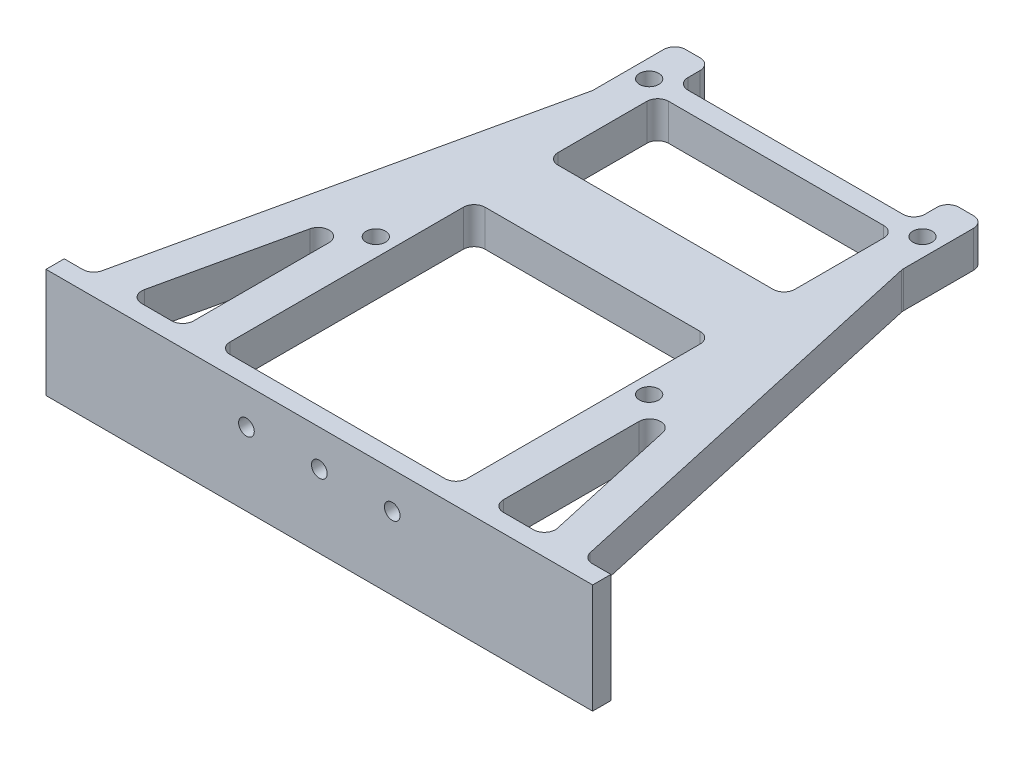
SolidWorks part; units mm, degrees
ref_plane "前视基准面" through (0, 0, 0) normal (0, 0, 1) x (1, 0, 0)
ref_plane "上视基准面" through (0, 0, 0) normal (0, 1, 0) x (1, 0, 0)
ref_plane "右视基准面" through (0, 0, 0) normal (1, 0, 0) x (0, 0, -1)
other "Configuration Table"
sketch "Sketch1" plane through (0, 0, 0) normal (0, 0, 1) x (1, 0, 0)
  line L1 (0, 0) -> (150, 0)
  line L2 (0, 0) -> (0, 30)
  line L3 (0, 30) -> (150, 30)
  line L4 (150, 0) -> (150, 30)
  dimension "D1" = 30
  dimension "D2" = 150
extrude "Boss-Extrude1" add sketch "Sketch1" along normal blind 5
sketch "Sketch2" plane through (0, 0, 5) normal (0, 0, 1) x (1, 0, 0)
  line L0 (150, 30) -> (0, 30) construction
  line L1 (0, 30) -> (0, 0) construction
  line L2 (75, 30) -> (75, 0) construction
  line L3 (0, 0) -> (150, 0) construction
  circle A0 centre (75, 20) radius 2.15
  circle A1 centre (55, 20) radius 2.15
  circle A2 centre (95, 20) radius 2.15
  point P12 (0, 0)
  point P15 (55, 10)
  point P16 (0, 0)
  dimension "D2" = 4.3
  dimension "D3" = 75
  dimension "D4" = 4.3
  dimension "D5" = 40
  dimension "D1" = 10
extrude "Cut-Extrude1" cut sketch "Sketch2" against normal through all
sketch "Sketch3" plane through (0, 30, 0) normal (0, 1, 0) x (1, 0, 0)
  line L0 (75, 0) -> (75, -5) construction
  line L1 (150, 0) -> (0, 0) construction
  line L2 (150, -5) -> (0, -5) construction
  line L3 (107.5, 0) -> (107.5, 135)
  line L8 (32.5, 0) -> (42.5, 0)
  line L9 (32.5, 0) -> (32.5, 135)
  line L10 (32.5, 135) -> (42.5, 135)
  line L11 (42.5, 0) -> (42.5, 135)
  line L12 (117.5, 135) -> (107.5, 135)
  line L13 (117.5, 0) -> (117.5, 135)
  line L14 (117.5, 0) -> (107.5, 0)
  dimension "D1" = 75
  dimension "D2" = 10
  dimension "D3" = 135
extrude "Boss-Extrude2" add sketch "Sketch3" against normal blind 10 contours L9 L8 L11 L10 | L3 L12 L13 L14
sketch "Sketch4" plane through (0, 30, 0) normal (0, 1, 0) x (1, 0, 0)
  line L0 (32.5, 112.5) -> (7.5, 0)
  line L1 (32.5, 0) -> (32.5, 135) construction
  line L2 (32.5, 0) -> (0, 0) construction
  line L3 (7.5, 0) -> (17.5, 0)
  line L4 (7.5, 0) -> (17.5, 0)
  line L5 (17.5, 0) -> (32.5, 67.5)
  line L6 (32.5, 67.5) -> (32.5, 112.5)
  line L7 (75, 0) -> (75, -5) construction
  line L8 (107.5, 0) -> (42.5, 0) construction
  line L9 (150, -5) -> (0, -5) construction
  line L10 (117.5, 67.5) -> (117.5, 112.5)
  line L11 (132.5, 0) -> (117.5, 67.5)
  line L12 (142.5, 0) -> (132.5, 0)
  line L13 (142.5, 0) -> (132.5, 0)
  line L14 (117.5, 112.5) -> (142.5, 0)
  line M7 (150, 0) -> (117.5, 0)
  line M8 (117.5, 0) -> (117.5, 135)
  line M14 (32.5, 135) -> (32.5, 0)
  line M15 (32.5, 0) -> (0, 0)
  dimension "D1" = 10
  dimension "D2" = 15
extrude "Boss-Extrude3" add sketch "Sketch4" against normal up to surface (10 mm away) contours L5 L0 M15 M14 | L14 L11 M8 M7 up to face at (112.5, 20, -67.5)
sketch "Sketch5" plane through (0, 30, 0) normal (0, 1, 0) x (1, 0, 0)
  line L0 (107.5, 0) -> (42.5, 0) construction
  line L1 (107.5, 0) -> (42.5, 0) construction
  line L4 (32.5, 0) -> (32.5, 67.5) construction
  circle A0 centre (37.5, 48) radius 2.65
  circle A1 centre (112.5, 48) radius 2.65
  circle A2 centre (112.5, 123) radius 2.65
  circle A3 centre (37.5, 123) radius 2.65
  point P4 (123.0822, 122.2497)
  point P7 (0, 0)
  dimension "D1" = 5.3
  dimension "D6" = 75
  dimension "D7" = 75
  dimension "D2" = 48
  dimension "D3" = 5
  dimension "D4" = 2
  dimension "D5" = 2
sketch "Sketch6" plane through (107.5, 0, 0) normal (-1, 0, 0) x (0, 0, 1)
  line L0 (-112.5, 30) -> (0, 30) construction
  line L1 (-90, 30) -> (-70, 30)
  line L2 (-90, 30) -> (-90, 20)
  line L3 (-90, 20) -> (-70, 20)
  line L4 (-70, 30) -> (-70, 20)
  line L5 (-112.5, 20) -> (0, 20) construction
  dimension "D1" = 20
  dimension "D2" = 45
extrude "Boss-Extrude4" add sketch "Sketch6" along normal up to surface (65 mm away) up to face at (42.5, 25, -67.5)
extrude "Cut-Extrude3" cut sketch "Sketch5" against normal blind 10
sketch "Sketch7" plane through (107.5, 0, 0) normal (-1, 0, 0) x (0, 0, 1)
  line L0 (-125.65, 20) -> (-120.35, 20) construction
  line L1 (-125.65, 20) -> (-120.35, 20)
  line L2 (-125.65, 20) -> (-125.65, 30)
  line L3 (-125.65, 30) -> (-120.35, 30)
  line L4 (-120.35, 30) -> (-120.35, 20)
extrude "Boss-Extrude5" add sketch "Sketch7" along normal up to next
fillet "Fillet1" radius 3 20 edges at (32.5, 25, -135) (32.5, 25, -112.5) (7.5, 25, 0) (17.5, 25, 0) (32.5, 25, -67.5) (32.5, 25, 0) (42.5, 25, 0) (42.5, 25, -70) (107.5, 25, -70) (107.5, 25, 0) (117.5, 25, 0) (117.5, 25, -67.5) (132.5, 25, 0) (142.5, 25, 0) (117.5, 25, -112.5) (117.5, 25, -135) (107.5, 25, -135) (42.5, 25, -135) (42.5, 25, -125.65) (107.5, 25, -125.65)
fillet "Fillet2" radius 3 4 edges at (42.5, 25, -90) (42.5, 25, -120.35) (107.5, 25, -120.35) (107.5, 25, -90)
